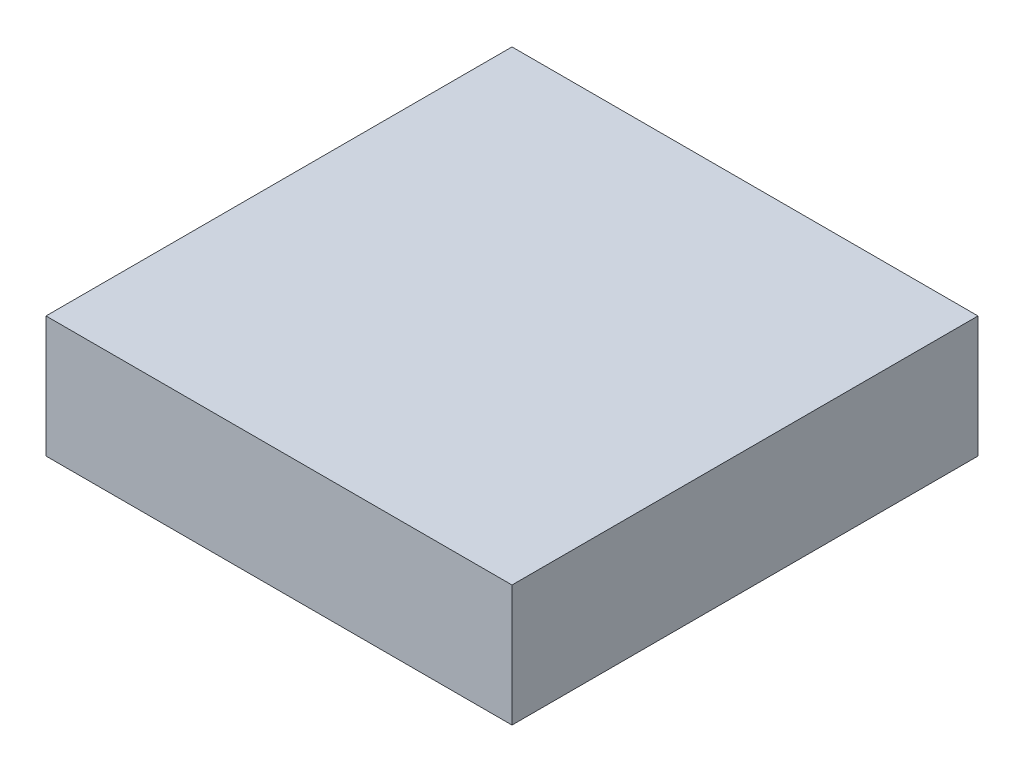
SolidWorks part; units mm, degrees
ref_plane "Front Plane" through (0, 0, 0) normal (0, 0, 1) x (1, 0, 0)
ref_plane "Top Plane" through (0, 0, 0) normal (0, 1, 0) x (1, 0, 0)
ref_plane "Right Plane" through (0, 0, 0) normal (1, 0, 0) x (0, 0, -1)
sketch "Sketch1" plane through (0, 0, 0) normal (0, 1, 0) x (1, 0, 0)
  line L1 (-48, 48) -> (48, 48)
  line L2 (-48, 48) -> (-48, -48)
  line L3 (-48, -48) -> (48, -48)
  line L4 (48, 48) -> (48, -48)
  dimension "D1" = 48
  dimension "D2" = 48
  dimension "D3" = 48
  dimension "D4" = 48
extrude "Boss-Extrude1" add sketch "Sketch1" along normal mid plane 25
